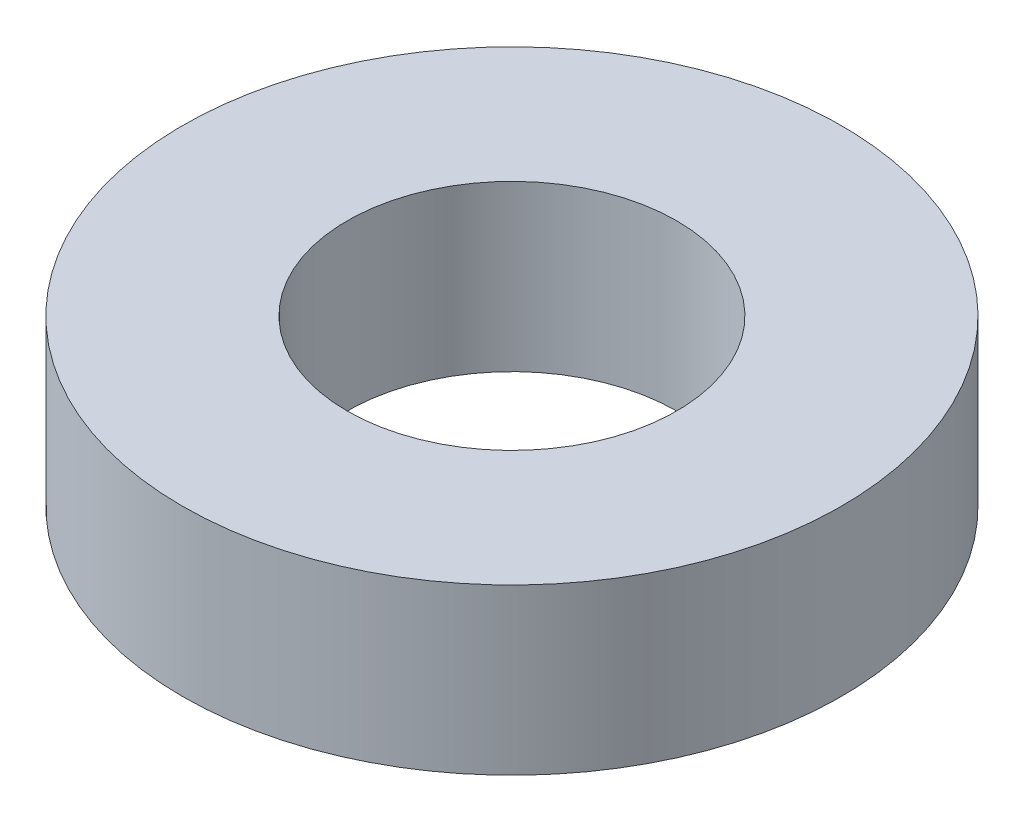
SolidWorks part; units mm, degrees
material "PET"
ref_plane "Front" through (0, 0, 0) normal (0, 0, 1) x (1, 0, 0)
ref_plane "Top" through (0, 0, 0) normal (0, 1, 0) x (1, 0, 0)
ref_plane "Right" through (0, 0, 0) normal (1, 0, 0) x (0, 0, -1)
sketch "Sketch1" plane through (0, 0, 0) normal (0, 1, 0) x (1, 0, 0)
  circle A1 centre (0, 0) radius 3.175
  circle A2 centre (0, 0) radius 6.35
  dimension "D2" = 3.175
  dimension "D1" = 6.35
extrude "Boss-Extrude2" add sketch "Sketch1" along normal blind 3.175
